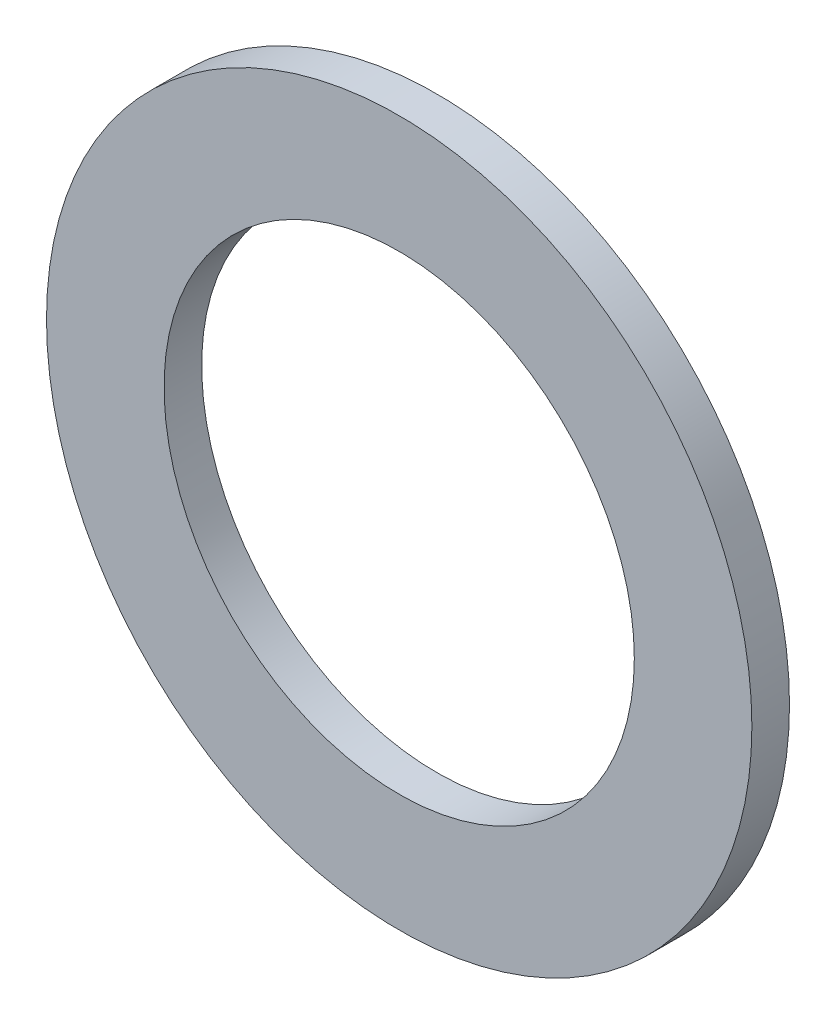
SolidWorks part; units mm, degrees
ref_plane "Front Plane" through (0, 0, 0) normal (0, 0, 1) x (1, 0, 0)
ref_plane "Top Plane" through (0, 0, 0) normal (0, 1, 0) x (1, 0, 0)
ref_plane "Right Plane" through (0, 0, 0) normal (1, 0, 0) x (0, 0, -1)
sketch "Sketch1" plane through (0, 0, 0) normal (0, 0, 1) x (1, 0, 0)
  circle A0 centre (0, 0) radius 1.5875
  circle A1 centre (0, 0) radius 2.3813
  dimension "OD" = 4.7625
  dimension "ID" = 3.175
sketch "Sketch2" plane through (0, 0, 0) normal (1, 0, 0) x (0, 0, -1)
  line L0 (-0.127, -2.3813) -> (0.127, -2.3813) construction
  line L1 (0, 2.3813) -> (0, -2.3813) construction
  point P3 (0, -2.3813)
sketch "Sketch3" plane through (0, 0, 0) normal (0, 0, 1) x (1, 0, 0)
  circle A0 centre (0, 0) radius 1.5875 construction
  circle A1 centre (0, 0) radius 2.3813 construction
  circle A2 centre (0, 0) radius 1.5875
  circle A3 centre (0, 0) radius 2.3813
extrude "Boss-Extrude1" add sketch "Sketch3" along normal mid plane 0.254
equation "\"D1@Boss-Extrude1\"=\"thickness@sketch2\""
